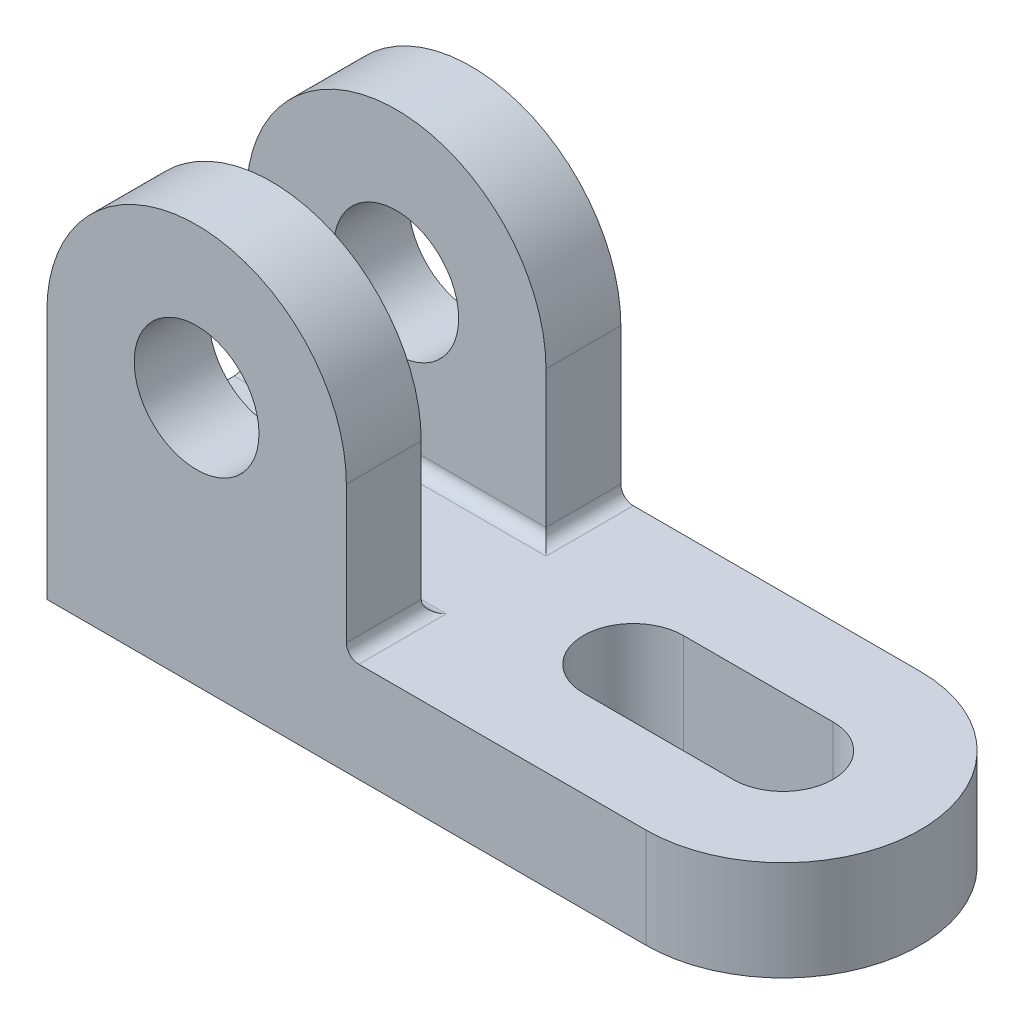
SolidWorks part; units mm, degrees
ref_plane "Front Plane" through (0, 0, 0) normal (0, 0, 1) x (1, 0, 0)
ref_plane "Top Plane" through (0, 0, 0) normal (0, 1, 0) x (1, 0, 0)
ref_plane "Right Plane" through (0, 0, 0) normal (1, 0, 0) x (0, 0, -1)
sketch "Sketch1" plane through (0, 0, 0) normal (0, 1, 0) x (1, 0, 0)
  line L1 (-59, 22) -> (59, 22)
  line L2 (-59, 22) -> (-59, -22)
  line L3 (-59, -22) -> (59, -22)
  line L4 (59, 22) -> (59, -22)
  line L5 (-59, 22) -> (59, -22) construction
  line L6 (-59, -22) -> (59, 22) construction
  circle A0 centre (37, 0) radius 22
  point P0 (0, 0)
  dimension "D1" = 118
  dimension "D2" = 44
extrude "Boss-Extrude1" add sketch "Sketch1" along normal blind 16 contours A0 L1 L2 L3 | A0
sketch "Sketch4" plane through (0, 16, 0) normal (0, 1, 0) x (1, 0, 0)
  line L0 (37, 0) -> (13, 0) construction
  line L1 (37, -8) -> (13, -8)
  line L2 (37, 8) -> (13, 8)
  arc A0 (37, -8) -> (37, 8) centre (37, 0) ccw
  arc A1 (13, 8) -> (13, -8) centre (13, 0) ccw
  point P4 (25, 0)
  dimension "D1" = 8
  dimension "D2" = 24
extrude "Cut-Extrude1" cut sketch "Sketch4" against normal blind 16
sketch "Sketch5" plane through (0, 0, 22) normal (0, 0, 1) x (1, 0, 0)
  line L0 (-59, 0) -> (37, 0) construction
  line L1 (-59, 16) -> (-11, 16)
  line L2 (-59, 16) -> (-59, 40)
  line L3 (-59, 40) -> (-11, 40)
  line L4 (-11, 16) -> (-11, 40)
  circle A0 centre (-35, 40) radius 24
  circle A1 centre (-35, 40) radius 10
  line M6 (37, 16) -> (-59, 16)
  dimension "D3" = 20
  dimension "D1" = 40
  dimension "D2" = 48
extrude "Boss-Extrude2" add sketch "Sketch5" against normal blind 12 contours A1 L3 A0 | A0 L2 L1 | A0 L4 M6 | A1 L3 A0
mirror "Mirror1" about plane through (0, 0, 0) normal (0, 0, 1) of "Boss-Extrude2"
fillet "Fillet1" radius 2 4 edges at (-35, 16, 10) (-35, 16, -10) (-11, 16, -16) (-11, 16, 16)
